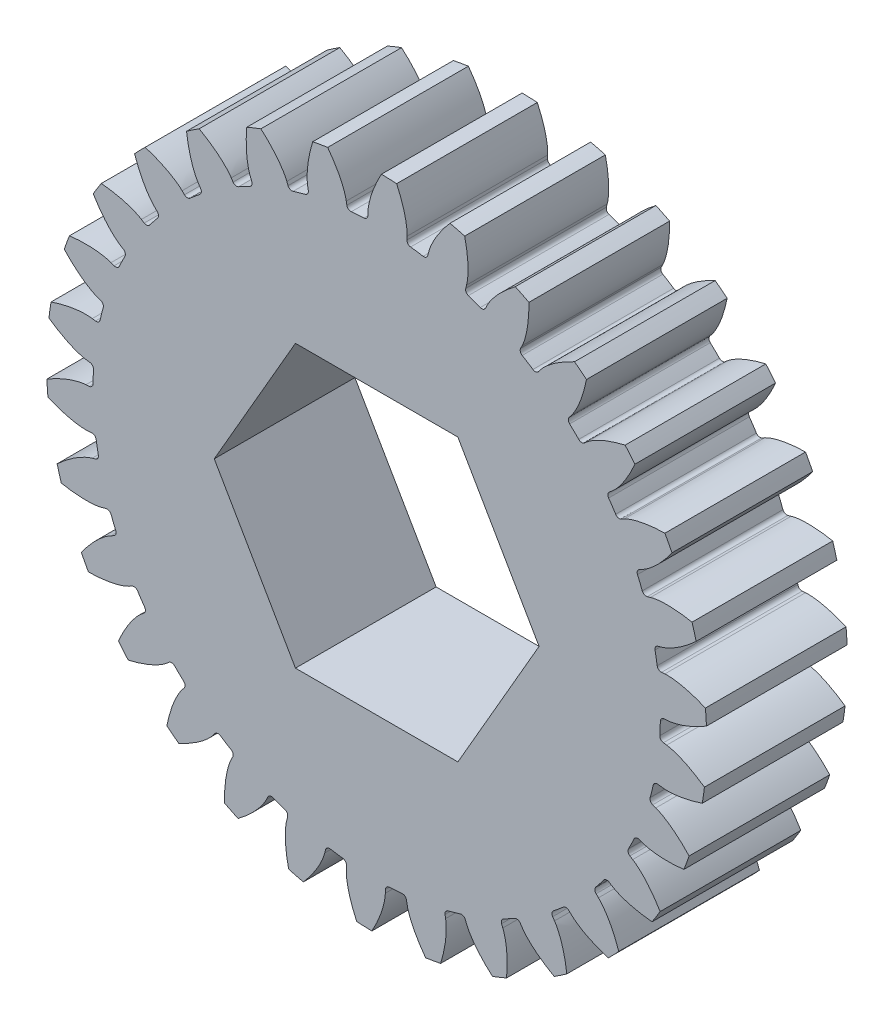
SolidWorks part; units mm, degrees
ref_plane "Front Plane" through (0, 0, 0) normal (0, 0, 1) x (1, 0, 0)
ref_plane "Top Plane" through (0, 0, 0) normal (0, 1, 0) x (1, 0, 0)
ref_plane "Right Plane" through (0, 0, 0) normal (1, 0, 0) x (0, 0, -1)
sketch "Sketch1" plane through (0, 0, 0) normal (0, 0, 1) x (1, 0, 0)
  line L0 (0, 0) -> (32.9254, 2.2181) construction
  circle A0 centre (0, 0) radius 30.25
  circle A1 centre (0, 0) radius 31.0099
  circle A2 centre (0, 0) radius 33 construction
  circle A3 centre (0, 0) radius 35.2
  arc A4 (32.9963, 0.4918) -> (32.7642, 3.9382) centre (0, 0) ccw
  spline S0 degree 4 poles (31.0099, 0) (31.0576, 0.0015) (31.153, 0.0074) (31.4195, 0.0389) (31.9214, 0.1374) (32.6755, 0.3542) (33.6783, 0.7504) (34.9156, 1.3757) (36.2888, 2.2432) (37.7039, 3.3305) (39.12, 4.6321) (40.4288, 6.041) (41.6327, 7.5402) (42.7883, 9.1941) (44.0802, 11.3326) (45.408, 14.0016) (46.6554, 17.2324) (47.6806, 20.9416) (48.3611, 24.7284) (48.7131, 28.5592) (48.7523, 32.4055) (48.5263, 35.7632) (48.1558, 38.6226) (47.7338, 40.9873) (47.3301, 42.8659) (46.8619, 44.7298) (46.3311, 46.5763) (45.7391, 48.4049) (45.1698, 49.9861) (44.6449, 51.3296) (44.2479, 52.2861) (43.9955, 52.8736) (43.7797, 53.3649) (43.5471, 53.8831) (43.3516, 54.3091) (42.9718, 55.1168) (42.6734, 55.7225) (42.2994, 56.4706) (41.9583, 57.1239) (41.5823, 57.8307) (41.2167, 58.4926) (40.9242, 59.012) (40.7344, 59.3398) (40.6354, 59.5106) knots 0 0 0 0 0 0.002802 0.005604 0.015718 0.02996 0.048734 0.068727 0.096889 0.125051 0.153212 0.181374 0.209535 0.237696 0.271429 0.327752 0.384075 0.440398 0.496721 0.553044 0.609367 0.66569 0.693852 0.722013 0.750174 0.778336 0.806497 0.834659 0.86282 0.876901 0.890982 0.895509 0.900036 0.909091 0.920455 0.931818 0.943182 0.954545 0.965909 0.977273 0.988636 1 1 1 1 1 construction
  spline S1 degree 4 poles (31.0099, 0) (31.0576, 0.0015) (31.153, 0.0074) (31.4195, 0.0389) (31.9214, 0.1374) (32.6755, 0.3542) (33.6783, 0.7504) (34.9156, 1.3757) (36.2888, 2.2432) (37.7039, 3.3305) (39.12, 4.6321) (40.4288, 6.041) (41.6327, 7.5402) (42.7883, 9.1941) (44.0802, 11.3326) (45.408, 14.0016) (46.6554, 17.2324) (47.6806, 20.9416) (48.3611, 24.7284) (48.7131, 28.5592) (48.7523, 32.4055) (48.5263, 35.7632) (48.1558, 38.6226) (47.7338, 40.9873) (47.3301, 42.8659) (46.8619, 44.7298) (46.3311, 46.5763) (45.7391, 48.4049) (45.1698, 49.9861) (44.6449, 51.3296) (44.2479, 52.2861) (43.9955, 52.8736) (43.7797, 53.3649) (43.6368, 53.6833) (43.5481, 53.8788) (43.4897, 54.0065) knots 0 0 0 0 0 0.002802 0.005604 0.015718 0.02996 0.048734 0.068727 0.096889 0.125051 0.153212 0.181374 0.209535 0.237696 0.271429 0.327752 0.384075 0.440398 0.496721 0.553044 0.609367 0.66569 0.693852 0.722013 0.750174 0.778336 0.806497 0.834659 0.86282 0.876901 0.890982 0.895509 0.900036 0.909091 0.909091 0.909091 0.909091 0.909091
  dimension "D1" = 60.5
  dimension "D2" = 62.0197
  dimension "D3" = 66
  dimension "D4" = 70.4
  dimension "D5" = 3.4558
extrude "Boss-Extrude1" add sketch "Sketch1" along normal mid plane 15 contours A0
sketch "Sketch4" plane through (0, 0, 0) normal (0, 0, 1) x (1, 0, 0)
  line L0 (0, 0) -> (32.9254, 2.2181) construction
  line L1 (0, 0) -> (32.9254, 2.2181) construction
  line L2 (31.0099, 0) -> (30.25, -0.0512)
  line L3 (30.7297, 4.1592) -> (29.9698, 4.108)
  circle A0 centre (0, 0) radius 31.0099 construction
  circle A1 centre (0, 0) radius 30.25 construction
  circle A2 centre (0, 0) radius 31.0099
  circle A3 centre (0, 0) radius 30.25
extrude "Boss-Extrude2" add sketch "Sketch4" along normal mid plane 15 contours L1 A3 L2 A2 | A3 L1 A2 L3
sketch "Sketch6" plane through (0, 0, 0) normal (0, 0, 1) x (1, 0, 0)
  line L0 (0, 0) -> (32.9254, 2.2181) construction
  line L1 (0, 0) -> (32.9254, 2.2181) construction
  circle A0 centre (0, 0) radius 31.0099 construction
  circle A1 centre (0, 0) radius 35.2 construction
  circle A2 centre (0, 0) radius 31.0099
  circle A3 centre (0, 0) radius 35.2
  spline S0 degree 4 poles (19.9798, -1999.4555) (22.4802, 64.9877) (25.7545, 1.2613) (28.8917, -0.4571) (31.9214, 0.1374) (32.6755, 0.3542) (33.6783, 0.7504) (34.9156, 1.3757) (36.2888, 2.2432) (37.7039, 3.3305) (39.12, 4.6321) (40.4288, 6.041) (41.6327, 7.5402) (42.7883, 9.1941) (44.0802, 11.3326) (45.408, 14.0016) (46.6554, 17.2324) (47.6806, 20.9416) (48.3611, 24.7284) (48.7131, 28.5592) (48.7523, 32.4055) (48.5263, 35.7632) (48.1558, 38.6226) (47.7338, 40.9873) (47.3301, 42.8659) (46.8619, 44.7298) (46.3311, 46.5763) (45.7391, 48.4049) (45.1698, 49.9861) (44.6449, 51.3296) (44.2479, 52.2861) (43.9955, 52.8736) (42.8987, 55.3706) (40.4315, 60.5154) (73.9045, -13.1683) (-789.1933, 1871.9335) knots -0.150874 -0.150874 -0.150874 -0.150874 -0.150874 0.002802 0.005604 0.015718 0.02996 0.048734 0.068727 0.096889 0.125051 0.153212 0.181374 0.209535 0.237696 0.271429 0.327752 0.384075 0.440398 0.496721 0.553044 0.609367 0.66569 0.693852 0.722013 0.750174 0.778336 0.806497 0.834659 0.86282 0.876901 0.890982 0.895509 0.900036 1.040494 1.040494 1.040494 1.040494 1.040494 only from (31.0099, 0) to (43.4897, 54.0065) construction
  spline S1 degree 4 poles (31.0099, 0) (31.0576, 0.0015) (31.153, 0.0074) (31.4195, 0.0389) (31.9214, 0.1374) (32.6755, 0.3542) (33.6783, 0.7504) (34.9156, 1.3757) (36.2888, 2.2432) (37.7039, 3.3305) (39.12, 4.6321) (40.4288, 6.041) (41.6327, 7.5402) (42.7883, 9.1941) (44.0802, 11.3326) (45.408, 14.0016) (46.6554, 17.2324) (47.6806, 20.9416) (48.3611, 24.7284) (48.7131, 28.5592) (48.7523, 32.4055) (48.5263, 35.7632) (48.1558, 38.6226) (47.7338, 40.9873) (47.3301, 42.8659) (46.8619, 44.7298) (46.3311, 46.5763) (45.7391, 48.4049) (45.1698, 49.9861) (44.6449, 51.3296) (44.2479, 52.2861) (43.9955, 52.8736) (43.7797, 53.3649) (43.6368, 53.6833) (43.5481, 53.8788) (43.4897, 54.0065) knots 0 0 0 0 0 0.002802 0.005604 0.015718 0.02996 0.048734 0.068727 0.096889 0.125051 0.153212 0.181374 0.209535 0.237696 0.271429 0.327752 0.384075 0.440398 0.496721 0.553044 0.609367 0.66569 0.693852 0.722013 0.750174 0.778336 0.806497 0.834659 0.86282 0.876901 0.890982 0.895509 0.900036 0.909091 0.909091 0.909091 0.909091 0.909091
  spline S2 degree 4 poles (30.7297, 4.1592) (30.7772, 4.1641) (30.8725, 4.171) (31.1408, 4.1755) (31.6514, 4.1452) (32.4278, 4.0315) (33.4747, 3.7734) (34.7846, 3.3197) (36.2618, 2.6443) (37.8099, 1.7566) (39.3878, 0.6566) (40.8738, -0.564) (42.2678, -1.8882) (43.6349, -3.3721) (45.2019, -5.318) (46.8757, -7.7848) (48.5451, -10.8191) (50.0585, -14.3573) (51.2408, -18.0186) (52.1035, -21.7676) (52.6582, -25.5738) (52.8845, -28.9315) (52.9009, -31.8148) (52.7999, -34.2147) (52.6518, -36.1305) (52.4378, -38.0403) (52.1595, -39.9414) (51.8181, -41.8329) (51.466, -43.4761) (51.126, -44.8779) (50.8609, -45.879) (50.6896, -46.495) (50.5416, -47.0108) (50.4427, -47.3455) (50.3811, -47.5512) (50.3403, -47.6855) knots 0 0 0 0 0 0.002802 0.005604 0.015718 0.02996 0.048734 0.068727 0.096889 0.125051 0.153212 0.181374 0.209535 0.237696 0.271429 0.327752 0.384075 0.440398 0.496721 0.553044 0.609367 0.66569 0.693852 0.722013 0.750174 0.778336 0.806497 0.834659 0.86282 0.876901 0.890982 0.895509 0.900036 0.909091 0.909091 0.909091 0.909091 0.909091
extrude "Boss-Extrude3" add sketch "Sketch6" along normal mid plane 15
fillet "Fillet1" radius 0.44 2 edges at (30.25, -0.0512, 0) (29.9698, 4.108, 0)
pattern_circular "CirPattern1" count 30 over 360 about axis through (0, 0, 7.5) along (0, 0, -1) of "Boss-Extrude3", "Boss-Extrude2", "Fillet1"
fillet "Fillet2" [suppressed] radius 0.44
pattern_circular "CirPattern2" [suppressed] count 30 over 360
sketch "Sketch7" plane through (0, 0, 7.5) normal (0, 0, 1) x (1, 0, 0)
  line L1 (8.6603, 15) -> (-8.6603, 15)
  line L2 (-8.6603, 15) -> (-17.3205, 0)
  line L3 (-17.3205, 0) -> (-8.6603, -15)
  line L4 (-8.6603, -15) -> (8.6603, -15)
  line L5 (8.6603, -15) -> (17.3205, 0)
  line L6 (17.3205, 0) -> (8.6603, 15)
  circle A0 centre (0, 0) radius 15 construction
  dimension "D1" = 30
extrude "Cut-Extrude1" cut sketch "Sketch7" against normal through all
equation "\"m\"= 2.2'Модуль"
equation "\"z\"= 30'Число зубьев"
equation "\"b\"= 15mm'Ширина зубчатого венца"
equation "\"a\"= 20 * pi / 180'Угол профиля исходного контура"
equation "\"D\"= \"m\" * \"z\"'Диаметр делительной окружности"
equation "\"Db\"= \"D\" * cos ( \"a\" )'Диаметр начальной окружности"
equation "\"Da\"= \"D\" + \"m\" * 2'Диаметр вершин зубьев"
equation "\"Df\"= \"D\" - \"m\" * 2.5'Диаметр впадин зубьев"
equation "\"S\"= \"m\" * pi / 2'Толщина зуба по дуге"
equation "\"D1@Sketch1\"= \"Df\""
equation "\"D2@Sketch1\"=\"Db\""
equation "\"D3@Sketch1\"=\"D\""
equation "\"D4@Sketch1\"=\"Da\""
equation "\"D1@Boss-Extrude1\"=\"b\""
equation "\"D5@Sketch1\"=\"S\""
equation "\"D1@Boss-Extrude2\"=\"b\""
equation "\"D1@Boss-Extrude3\"=\"b\""
equation "\"D1@Fillet1\"=\"m\"*0.2"
equation "\"D1@CirPattern1\"=\"z\""
equation "\"Fillet1\"= IIF ( \"Df\" > \"Db\" , \"suppressed\" , \"unsuppressed\" )"
equation "\"CirPattern1\"= IIF ( \"Df\" > \"Db\" , \"suppressed\" , \"unsuppressed\" )"
equation "\"D1@Fillet2\"=\"m\"*0.2"
equation "\"D1@CirPattern2\"=\"z\""
equation "\"Fillet2\"= IIF ( \"Db\" > \"Df\" , \"suppressed\" , \"unsuppressed\" )"
equation "\"CirPattern2\"= IIF ( \"Db\" > \"Df\" , \"suppressed\" , \"unsuppressed\" )"
